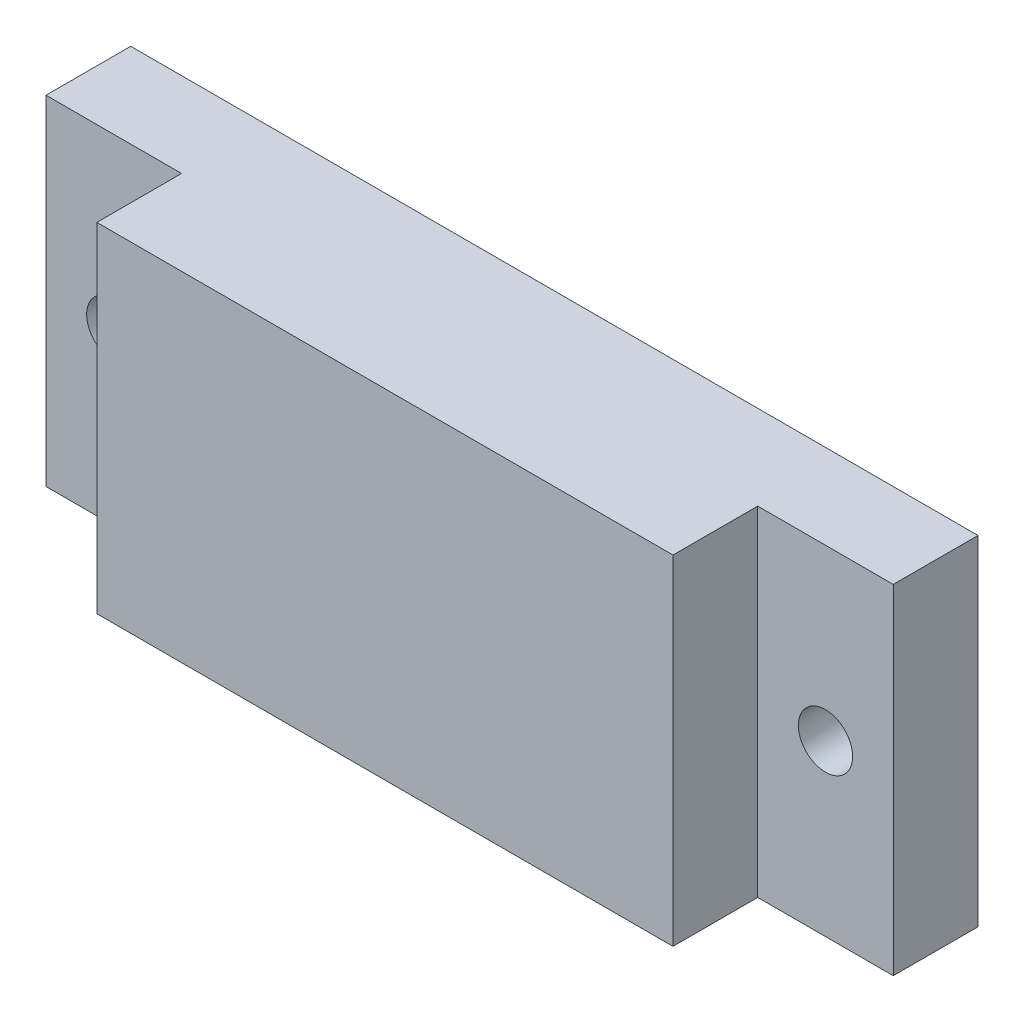
SolidWorks part; units mm, degrees
ref_plane "前视基准面" through (0, 0, 0) normal (0, 0, 1) x (1, 0, 0)
ref_plane "上视基准面" through (0, 0, 0) normal (0, 1, 0) x (1, 0, 0)
ref_plane "右视基准面" through (0, 0, 0) normal (1, 0, 0) x (0, 0, -1)
sketch "草图1" plane through (0, 0, 0) normal (0, 0, 1) x (1, 0, 0)
  line L0 (-9.2657, 25.3497) -> (40.7343, 25.3497)
  line L1 (40.7343, 25.3497) -> (40.7343, 5.3497)
  line L2 (-9.2657, 25.3497) -> (-9.2657, 5.3497)
  line L3 (-9.2657, 5.3497) -> (40.7343, 5.3497)
  dimension "D1" = 50
  dimension "D2" = 20
extrude "凸台-拉伸1" add sketch "草图1" along normal blind 5
sketch "草图2" plane through (0, 0, 5) normal (0, 0, 1) x (1, 0, 0)
  line L0 (-9.2657, 25.3497) -> (-1.2657, 25.3497) construction
  line L1 (40.7343, 25.3497) -> (-9.2657, 25.3497) construction
  line L2 (-1.2657, 25.3497) -> (32.7343, 25.3497)
  line L3 (-1.2657, 25.3497) -> (-1.2657, 5.3497)
  line L4 (-9.2657, 5.3497) -> (40.7343, 5.3497) construction
  line L5 (-1.2657, 5.3497) -> (32.7343, 5.3497)
  line L6 (32.7343, 5.3497) -> (32.7343, 25.3497)
  dimension "D1" = 8
  dimension "D2" = 34
extrude "凸台-拉伸2" add sketch "草图2" along normal blind 5
sketch "草图3" plane through (0, 0, 5) normal (0, 0, 1) x (1, 0, 0)
  line L0 (-9.2657, 25.3497) -> (-5.2657, 25.3497) construction
  line L1 (-1.2657, 25.3497) -> (-9.2657, 25.3497) construction
  line L2 (-5.2657, 25.3497) -> (-5.2657, 15.3497) construction
  line L5 (15.7343, 25.3497) -> (15.7343, 2.7876) construction
  circle A0 centre (-5.2657, 15.3497) radius 1.6
  circle A1 centre (36.7343, 15.3497) radius 1.6
  dimension "D3" = 3.2
  dimension "D1" = 4
  dimension "D2" = 10
extrude "切除-拉伸1" cut sketch "草图3" against normal blind 5
